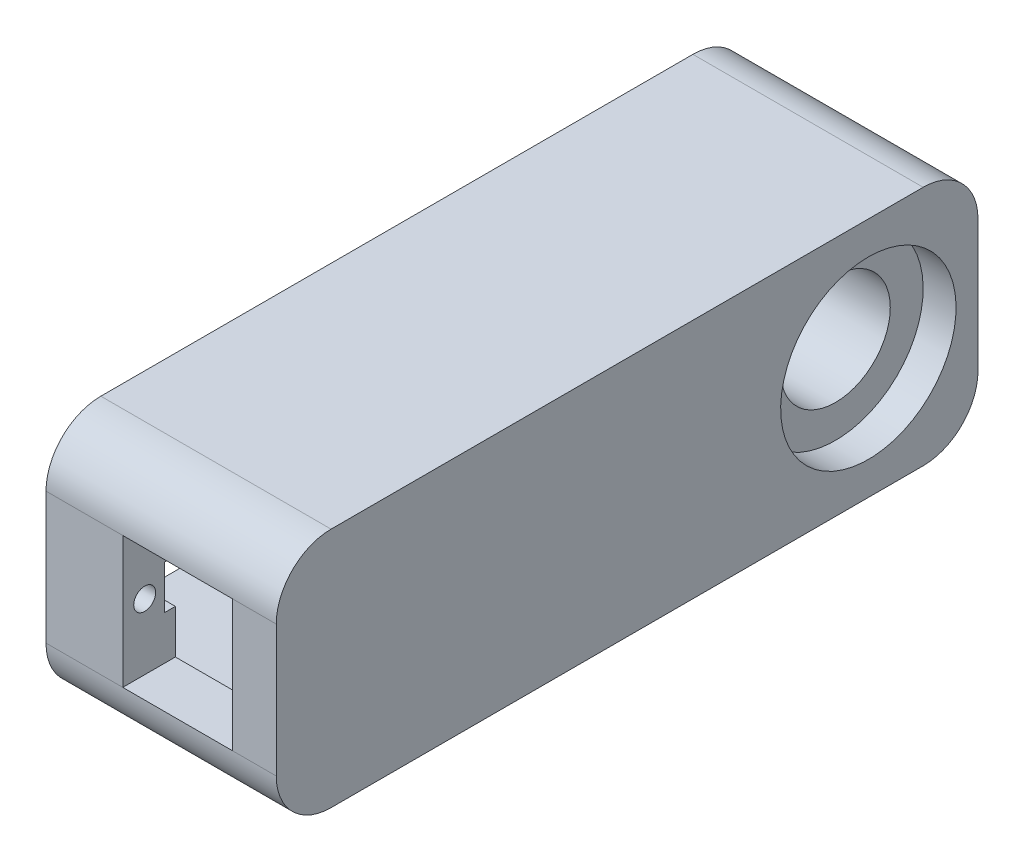
SolidWorks part; units mm, degrees
ref_plane "Front Plane" through (0, 0, 0) normal (0, 0, 1) x (1, 0, 0)
ref_plane "Top Plane" through (0, 0, 0) normal (0, 1, 0) x (1, 0, 0)
ref_plane "Right Plane" through (0, 0, 0) normal (1, 0, 0) x (0, 0, -1)
sketch "Sketch1" plane through (54.1122, 0, 0) normal (1, 0, 0) x (0, 0, -1)
  line L4 (66.5, 65.0424) -> (76.5, 65.0424) construction
  line L12 (12.5, 76.0424) -> (12.5, 54.0424)
  line L13 (12.5, 54.0424) -> (76.5, 54.0424)
  line L14 (76.5, 54.0424) -> (76.5, 76.0424)
  line L15 (76.5, 76.0424) -> (12.5, 76.0424)
  circle A0 centre (66.5, 65.0424) radius 5 construction
  dimension "D1" = 10
  dimension "D2" = 10
  dimension "D3" = 22
extrude "Boss-Extrude1" add sketch "Sketch1" along normal blind 4 and the other way up to surface (17 mm away)
sketch "Sketch2" plane through (0, 0, -12.5) normal (0, 0, 1) x (1, 0, 0)
  line L0 (54.1122, 59.0424) -> (37.1122, 59.0424) construction
  line L1 (54.1122, 71.0424) -> (44.1122, 71.0424)
  line L2 (54.1122, 71.0424) -> (54.1122, 59.0424)
  line L3 (54.1122, 59.0424) -> (44.1122, 59.0424)
  line L4 (44.1122, 71.0424) -> (44.1122, 59.0424)
  dimension "D1" = 10
extrude "Cut-Extrude1" cut sketch "Sketch2" against normal blind 5
sketch "Sketch3" plane through (37.1122, 0, 0) normal (-1, 0, 0) x (0, 0, 1)
  circle A0 centre (-14.5, 65.0424) radius 1
  circle A1 centre (-42.5, 65.0424) radius 1
  dimension "D1" = 2
extrude "Cut-Extrude2" cut sketch "Sketch3" against normal up to surface (7 mm away) up to face at (44.1122, 65.0424, -15)
sketch "Sketch4" plane through (37.1122, 0, 0) normal (-1, 0, 0) x (0, 0, 1)
  line L0 (-76.5, 65.0424) -> (-66.5, 65.0424) construction
  line L2 (-76.5, 54.0424) -> (-76.5, 76.0424) construction
  line L4 (-66.5, 65.0424) -> (-66.5, 76.0424) construction
  line L5 (-76.5, 76.0424) -> (-12.5, 76.0424) construction
  circle A3 centre (-66.5, 65.0424) radius 5
  dimension "D1" = 10
  dimension "D2" = 10
extrude "Cut-Extrude3" cut sketch "Sketch4" against normal up to surface (21 mm away) up to face at (58.1122, 65.0424, -44.5)
ref_plane "Plane1" through (29.1122, 0, 0) normal (1, 0, 0) x (0, 0, -1)
sketch "Sketch7" plane through (37.1122, 0, 0) normal (-1, 0, 0) x (0, 0, 1)
  line L0 (-39.7, 71.2424) -> (-17.3, 71.2424)
  line L1 (-39.5, 71.0424) -> (-17.5, 71.0424) construction
  line L2 (-39.5, 71.0424) -> (-39.5, 59.0424) construction
  line L3 (-39.5, 59.0424) -> (-17.5, 59.0424) construction
  line L4 (-17.5, 71.0424) -> (-17.5, 59.0424) construction
  line L5 (-17.3, 71.2424) -> (-17.3, 58.8424)
  line L6 (-39.7, 58.8424) -> (-17.3, 58.8424)
  line L7 (-39.7, 71.2424) -> (-39.7, 58.8424)
  dimension "D1" = 0.2
extrude "Cut-Extrude4" cut sketch "Sketch7" against normal up to vertex
sketch "Sketch8" plane through (44.1122, 0, 0) normal (1, 0, 0) x (0, 0, -1)
  line L0 (14.5, 65.0424) -> (17.3, 65.0424) construction
  line L1 (17.3, 59.0424) -> (17.3, 71.0424) construction
  line L2 (17.3, 63.0424) -> (17.3, 67.0424) construction
  line L4 (17.3, 63.0424) -> (16.3, 63.0424)
  line L5 (17.3, 63.0424) -> (17.3, 67.0424)
  line L6 (17.3, 67.0424) -> (16.3, 67.0424)
  line L7 (16.3, 63.0424) -> (16.3, 67.0424)
  point P8 (17.3, 65.0424)
  dimension "D1" = 4
  dimension "D2" = 1
extrude "Cut-Extrude5" cut sketch "Sketch8" against normal up to next
sketch "Sketch10" plane through (58.1122, 0, 0) normal (1, 0, 0) x (0, 0, -1)
  line L1 (17.5, 76.0424) -> (71.5, 76.0424) construction
  line L2 (12.5, 71.0424) -> (12.5, 59.0424) construction
  line L3 (17.5, 54.0424) -> (71.5, 54.0424) construction
  line L4 (76.5, 71.0424) -> (76.5, 59.0424) construction
  arc A0 (76.5, 71.0424) -> (71.5, 76.0424) centre (71.5, 71.0424) ccw
  arc A1 (76.5, 59.0424) -> (71.5, 54.0424) centre (71.5, 59.0424) cw
  arc A2 (12.5, 59.0424) -> (17.5, 54.0424) centre (17.5, 59.0424) ccw
  arc A3 (17.5, 76.0424) -> (12.5, 71.0424) centre (17.5, 71.0424) ccw
  point P10 (76.5, 54.0424)
  point P15 (12.5, 76.0424)
  line M10 (76.5, 76.0424) -> (12.5, 76.0424)
  line M11 (12.5, 76.0424) -> (12.5, 54.0424)
  line M12 (12.5, 54.0424) -> (76.5, 54.0424)
  line M13 (76.5, 54.0424) -> (76.5, 76.0424)
  dimension "D1" = 5
extrude "Cut-Extrude7" cut sketch "Sketch10" against normal blind 21 contours A3 M10 M11 | A0 M13 M10 | A1 M13 M12 | A2 M11 M12
sketch "Sketch9" plane through (58.1122, 0, 0) normal (1, 0, 0) x (0, 0, -1)
  line L0 (76.5, 65.0424) -> (74.5, 65.0424) construction
  line L1 (76.5, 59.0424) -> (76.5, 71.0424) construction
  circle A0 centre (66.5, 65.0424) radius 8
  dimension "D1" = 2
extrude "Cut-Extrude6" cut sketch "Sketch9" against normal blind 3
move or copy body "Body-Move/Copy1" [suppressed] bodies to move or copy 106
